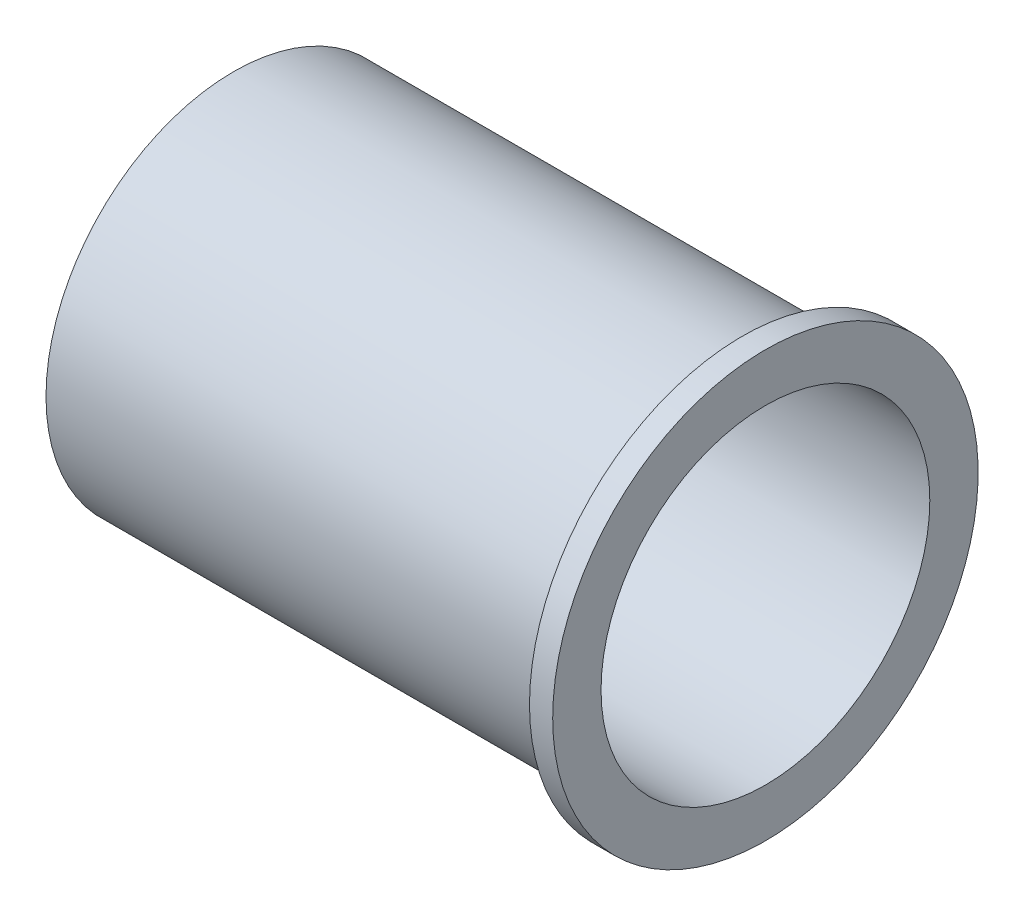
SolidWorks part; units mm, degrees
material "Brass"
ref_plane "Front Plane" through (0, 0, 0) normal (0, 0, 1) x (1, 0, 0)
ref_plane "Top Plane" through (0, 0, 0) normal (0, 1, 0) x (1, 0, 0)
ref_plane "Right Plane" through (0, 0, 0) normal (1, 0, 0) x (0, 0, -1)
sketch "Sketch1" plane through (0, 0, 0) normal (0, 0, 1) x (1, 0, 0)
  line L0 (-94.8899, 0) -> (0, 0) construction
  line L1 (0, 0) -> (0, 77.2484) construction
  line L2 (-137.5, 42.5) -> (0, 42.5)
  line L3 (0, 42.5) -> (0, 55)
  line L4 (-137.5, 48.5) -> (-6, 48.5)
  line L5 (-6, 48.5) -> (-6, 55)
  line L6 (0, 55) -> (-6, 55)
  line L7 (-137.5, 48.5) -> (-137.5, 42.5)
  dimension "D1" = 85
  dimension "D2" = 110
  dimension "D3" = 137.5
  dimension "D4" = 6
revolve "Revolve1" add sketch "Sketch1" angle 360 about L0
